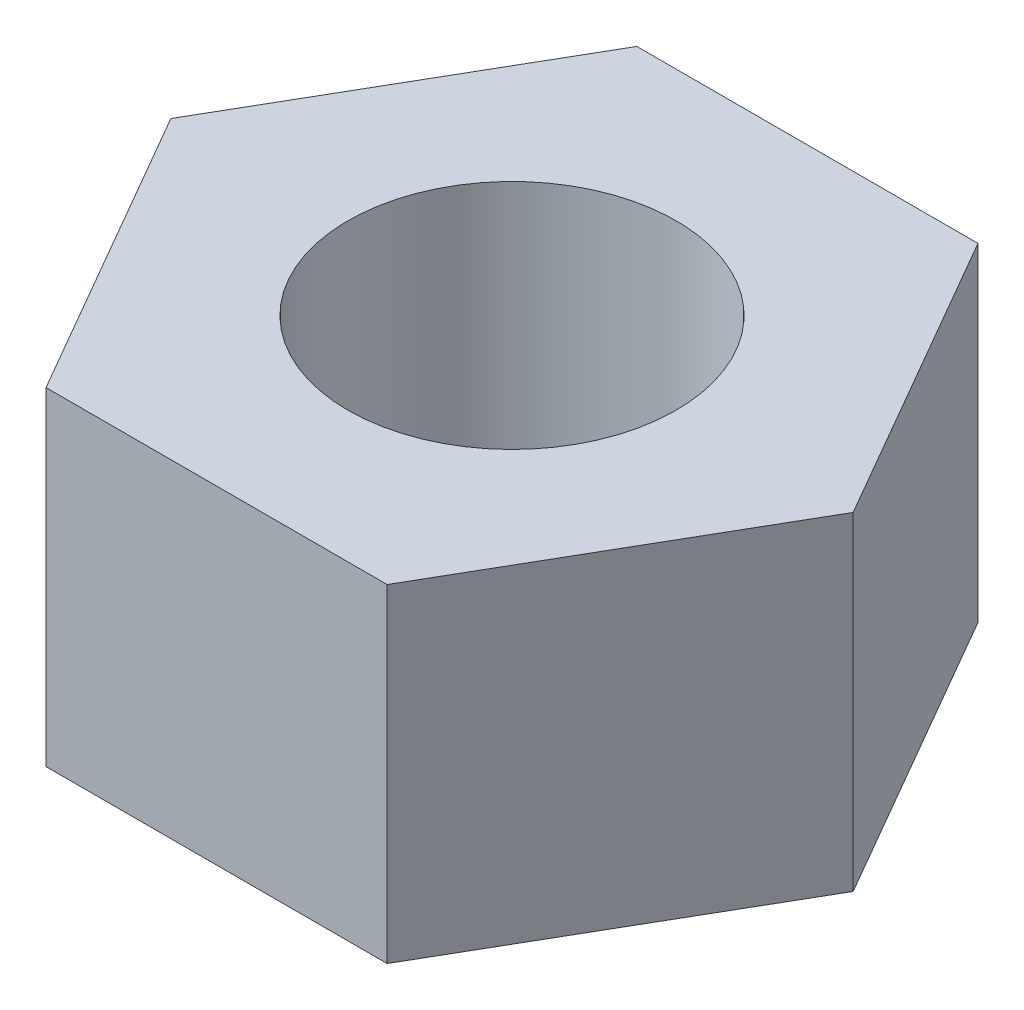
SolidWorks part; units mm, degrees
ref_plane "Front Plane" through (0, 0, 0) normal (0, 0, 1) x (1, 0, 0)
ref_plane "Top Plane" through (0, 0, 0) normal (0, 1, 0) x (1, 0, 0)
ref_plane "Right Plane" through (0, 0, 0) normal (1, 0, 0) x (0, 0, -1)
sketch "Sketch2" plane through (0, 0, 0) normal (0, 1, 0) x (1, 0, 0)
  line L0 (-179.1885, 0) -> (223.5377, 0) construction
  line L2 (4.6765, 8.1) -> (-4.6765, 8.1)
  line L3 (-4.6765, 8.1) -> (-9.3531, 0)
  line L4 (-9.3531, 0) -> (-4.6765, -8.1)
  line L5 (-4.6765, -8.1) -> (4.6765, -8.1)
  line L6 (4.6765, -8.1) -> (9.3531, 0)
  line L7 (9.3531, 0) -> (4.6765, 8.1)
  circle A0 centre (0, 0) radius 8.1 construction
  circle A1 centre (0, 0) radius 4.5
  dimension "D1" = 9
  dimension "D2" = 16.2
extrude "Boss-Extrude1" add sketch "Sketch2" along normal blind 9
